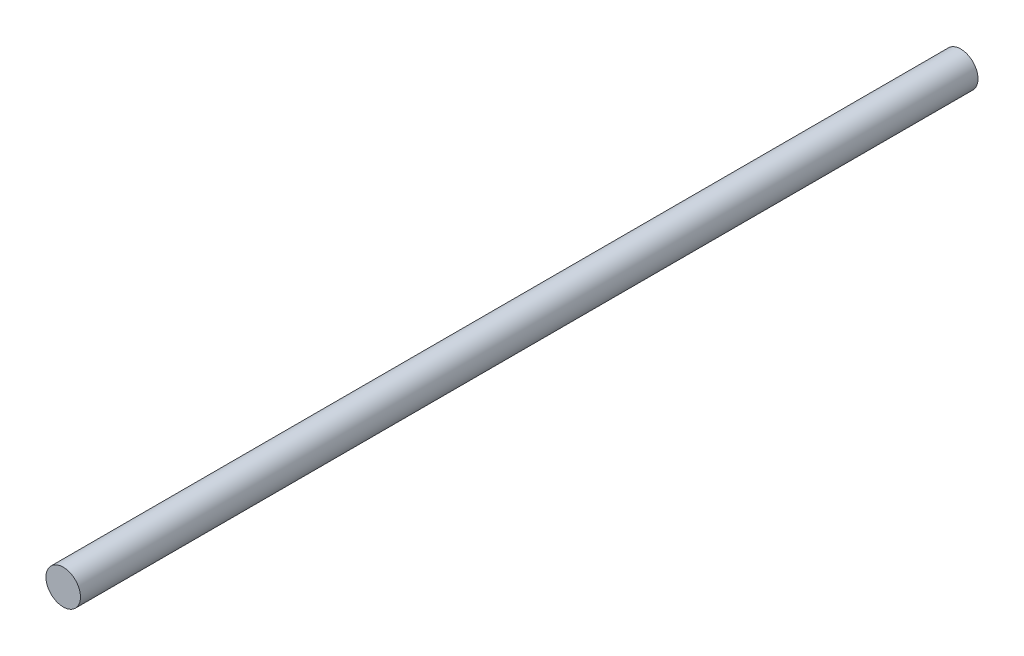
SolidWorks part; units mm, degrees
ref_plane "Front Plane" through (0, 0, 0) normal (0, 0, 1) x (1, 0, 0)
ref_plane "Top Plane" through (0, 0, 0) normal (0, 1, 0) x (1, 0, 0)
ref_plane "Right Plane" through (0, 0, 0) normal (1, 0, 0) x (0, 0, -1)
sketch "Sketch1" plane through (0, 0, 0) normal (0, 0, 1) x (1, 0, 0)
  circle A0 centre (0, 0) radius 3.175
  dimension "D1" = 6.35
extrude "Boss-Extrude1" add sketch "Sketch1" along normal blind 165.1
